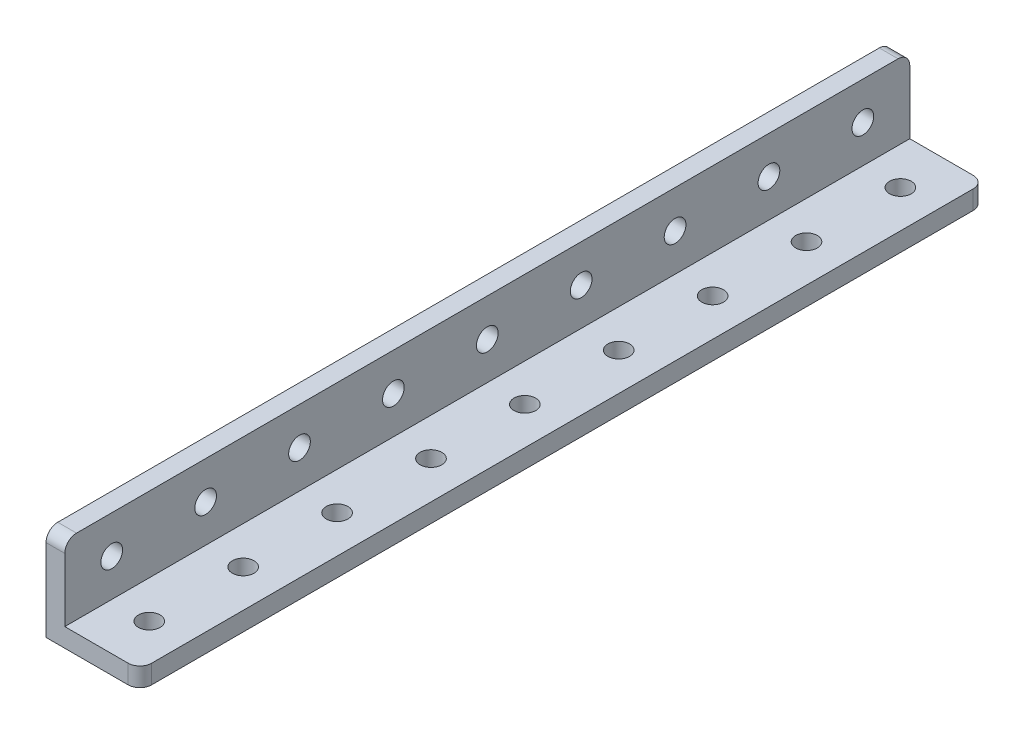
SolidWorks part; units mm, degrees
material "2024 Alloy"
ref_plane "Front Plane" through (0, 0, 0) normal (0, 0, 1) x (1, 0, 0)
ref_plane "Top Plane" through (0, 0, 0) normal (0, 1, 0) x (1, 0, 0)
ref_plane "Right Plane" through (0, 0, 0) normal (1, 0, 0) x (0, 0, -1)
ref_plane "Plane1" through (16, 0, 0) normal (1, 0, 0) x (0, 0, -1)
sketch "Sketch1" plane through (16, 0, 0) normal (1, 0, 0) x (0, 0, -1)
  line L0 (0, 0) -> (144, 0)
  line L1 (144, 0) -> (144, 16)
  line L2 (144, 16) -> (0, 16)
  line L3 (0, 16) -> (0, 0)
extrude "Boss-Extrude1" add sketch "Sketch1" against normal blind 16
sketch "Sketch2" plane through (0, 0, 0) normal (0, 0, 1) x (1, 0, 0)
  line L0 (3.2, 3.2) -> (16, 3.2)
  line L1 (16, 3.2) -> (16, 16)
  line L2 (16, 16) -> (3.2, 16)
  line L3 (3.2, 16) -> (3.2, 3.2)
extrude "Cut-Extrude1" cut sketch "Sketch2" against normal through all
hole_wizard "Ø3.7 (3.7) Diameter Hole1" positions "Sketch4" profile "Sketch3" hole size "Ø3.7" standard "ANSI Metric"
sketch "Sketch4" plane through (0, 0, 0) normal (-1, 0, 0) x (0, 0, 1)
  point P0 (-24, 9.6)
  point P1 (-40, 9.6)
  point P2 (-56, 9.6)
  point P3 (-72, 9.6)
  point P4 (-88, 9.6)
  point P5 (-104, 9.6)
  point P6 (-120, 9.6)
  point P7 (-136, 9.6)
  point P8 (-8, 9.6)
sketch "Sketch3" plane through (0, 9.6, -24) normal (0, 1, 0) x (0, 0, 1)
  line L0 (0, 0) -> (0, 16)
  line L1 (0, 16) -> (1.85, 16)
  line L2 (1.85, 16) -> (1.85, 0)
  line L5 (1.85, 0) -> (0, 0)
  line L11 (0, -6.35) -> (0, 107.95) construction
  dimension "Thru Hole Dia." = 3.7
  dimension "Thru Hole Depth" = 16
hole_wizard "Ø3.7 (3.7) Diameter Hole2" positions "Sketch6" profile "Sketch5" hole size "Ø3.7" standard "ANSI Metric"
sketch "Sketch6" plane through (0, 0, 0) normal (0, -1, 0) x (-1, 0, 0)
  point P0 (-9.6, 24)
  point P1 (-9.6, 40)
  point P2 (-9.6, 56)
  point P3 (-9.6, 72)
  point P4 (-9.6, 88)
  point P5 (-9.6, 104)
  point P6 (-9.6, 120)
  point P7 (-9.6, 136)
  point P8 (-9.6, 8)
sketch "Sketch5" plane through (9.6, 0, -24) normal (1, 0, 0) x (0, 0, -1)
  line L0 (0, 0) -> (0, 16)
  line L1 (0, 16) -> (1.85, 16)
  line L2 (1.85, 16) -> (1.85, 0)
  line L5 (1.85, 0) -> (0, 0)
  line L11 (0, -6.35) -> (0, 107.95) construction
  dimension "Thru Hole Dia." = 3.7
  dimension "Thru Hole Depth" = 16
fillet "Fillet1" radius 2 4 edges at (1.6, 16, -144) (1.6, 16, 0) (16, 1.6, -144) (16, 1.6, 0)
